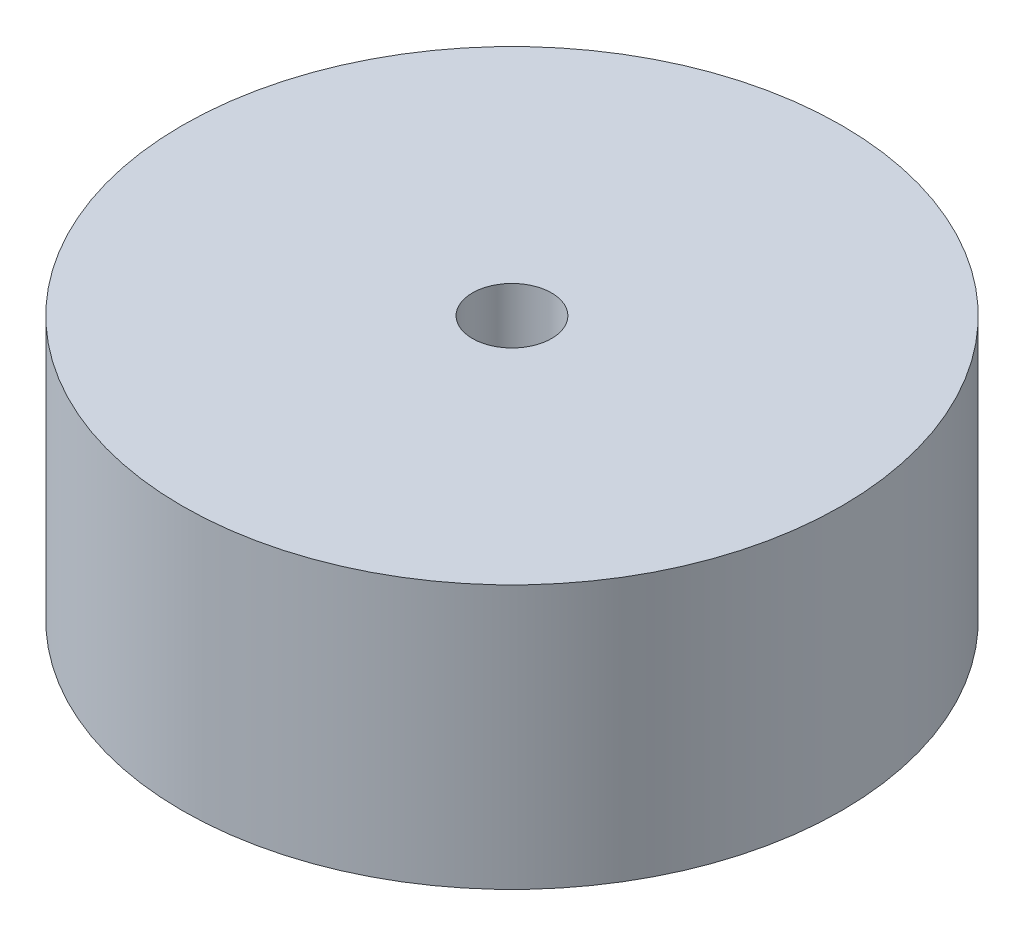
SolidWorks part; units mm, degrees
ref_plane "Front Plane" through (0, 0, 0) normal (0, 0, 1) x (1, 0, 0)
ref_plane "Top Plane" through (0, 0, 0) normal (0, 1, 0) x (1, 0, 0)
ref_plane "Right Plane" through (0, 0, 0) normal (1, 0, 0) x (0, 0, -1)
sketch "Sketch1" plane through (0, 0, 0) normal (0, 1, 0) x (1, 0, 0)
  circle A0 centre (0, 0) radius 3.048
  circle A1 centre (0, 0) radius 25.4
  dimension "D1" = 6.096
  dimension "D2" = 50.8
extrude "Boss-Extrude1" add sketch "Sketch1" along normal blind 20.32
